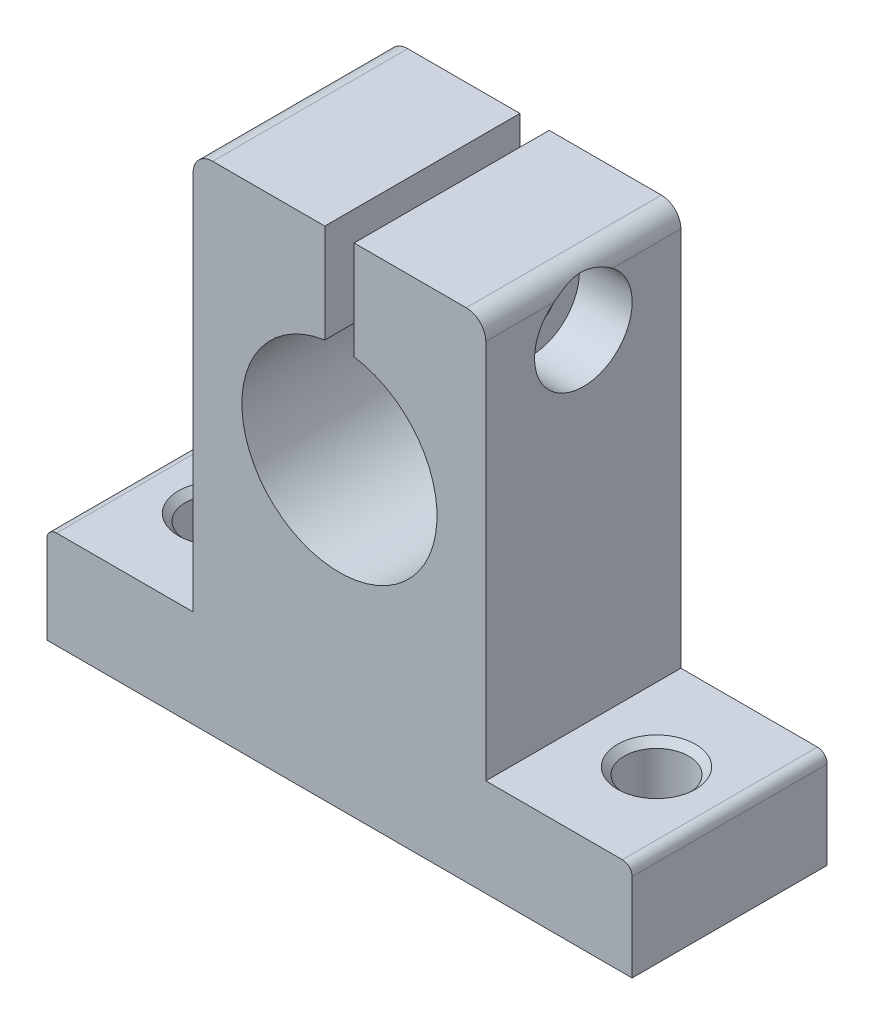
SolidWorks part; units mm, degrees
ref_plane "Front Plane" through (0, 0, 0) normal (0, 0, 1) x (1, 0, 0)
ref_plane "Top Plane" through (0, 0, 0) normal (0, 1, 0) x (1, 0, 0)
ref_plane "Right Plane" through (0, 0, 0) normal (1, 0, 0) x (0, 0, -1)
sketch "Sketch1" plane through (0, 0, 0) normal (0, 0, 1) x (1, 0, 0)
  line L0 (0, 0) -> (0, 64.1906) construction
  line L1 (30, 0) -> (-30, 0)
  line L2 (-30, 0) -> (-30, 9)
  line L3 (-29, 10) -> (-15, 10)
  line L4 (-15, 10) -> (-15, 49)
  line L5 (-13, 51) -> (-1.5, 51)
  line L6 (-1.5, 51) -> (-1.5, 40.8869)
  line L7 (1.5, 51) -> (1.5, 40.8869)
  line L8 (13, 51) -> (1.5, 51)
  line L9 (15, 10) -> (15, 49)
  line L10 (29, 10) -> (15, 10)
  line L11 (30, 0) -> (30, 9)
  arc A0 (-1.5, 40.8869) -> (1.5, 40.8869) centre (0, 31) ccw
  arc A1 (-30, 9) -> (-29, 10) centre (-29, 9) cw
  arc A2 (-15, 49) -> (-13, 51) centre (-13, 49) cw
  arc A3 (15, 49) -> (13, 51) centre (13, 49) ccw
  arc A4 (30, 9) -> (29, 10) centre (29, 9) ccw
  dimension "D1" = 20
  dimension "D5" = 1
  dimension "D9" = 2
  dimension "D2" = 31
  dimension "D4" = 51
  dimension "D6" = 15
  dimension "D7" = 30
  dimension "D8" = 1.5
extrude "Boss-Extrude1" add sketch "Sketch1" along normal blind 20
sketch "Sketch2" plane through (15, 0, 0) normal (1, 0, 0) x (0, 0, -1)
  line L0 (-10, 51) -> (-10, 0) construction
  line L1 (-20, 51) -> (0, 51) construction
  line L2 (-20, 0) -> (0, 0) construction
  line L3 (-10, 45) -> (-20, 45) construction
  line L4 (-20, 10) -> (-20, 49) construction
  dimension "D1" = 6
sketch "Sketch3" plane through (0, 10, 0) normal (0, 1, 0) x (1, 0, 0)
  line L0 (-30, -10) -> (30, -10) construction
  line L1 (-30, -20) -> (-30, 0) construction
  line L2 (30, -20) -> (30, 0) construction
  line L3 (0, 0) -> (0, -25.2345) construction
  circle A0 centre (-22.5, -10) radius 4.3189
  circle A1 centre (22.5, -10) radius 4.3189
  dimension "D1" = 22.5
hole_wizard "CSK for M6 Hex Socket Countersunk Cap Screw1" positions "3DSketch1" profile "Sketch4" countersink size "M6" standard "ISO" end condition through all
sketch3d "3DSketch1"
  point P0 (-22.5, 10, 10)
  point P3 (22.5, 10, 10)
sketch "Sketch4" plane through (-22.5, 10, 10) normal (1, 0, 0) x (0, 0, 1)
  line L0 (0, 0) -> (0, 10)
  line L1 (0, 10) -> (3.3, 10)
  line L2 (3.3, 10) -> (3.3, 0.7)
  line L3 (3.3, 0.7) -> (4, 0)
  line L5 (4, 0) -> (0, 0)
  line L6 (-3.3, 0.7) -> (-4, 0) construction
  line L11 (0, -6.35) -> (0, 107.95) construction
  dimension "Thru Hole Dia." = 6.6
  dimension "Thru Hole Depth" = 10
  dimension "Near C'Sink Dia." = 8
  dimension "Near C'Sink Angle" = 90
hole_wizard "CBORE for M5 Hex Socket Head Cap Screw1" positions "3DSketch2" profile "Sketch5" counterbore size "M5" standard "ISO" end condition through all
sketch3d "3DSketch2"
  point P0 (15, 45, 10)
sketch "Sketch5" plane through (15, 45, 10) normal (0, 1, 0) x (0, 0, -1)
  line L0 (0, 0) -> (0, 45)
  line L1 (0, 45) -> (2.75, 45)
  line L3 (2.75, 45) -> (2.75, 5.4)
  line L4 (2.75, 5.4) -> (5, 5.4)
  line L5 (5, 5.4) -> (5, 0)
  line L7 (5, 0) -> (0, 0)
  line L11 (0, -6.35) -> (0, 107.95) construction
  dimension "Thru Hole Dia." = 5.5
  dimension "Thru Hole Depth" = 45
  dimension "C'Bore Dia." = 10
  dimension "C'Bore Depth" = 5.4
